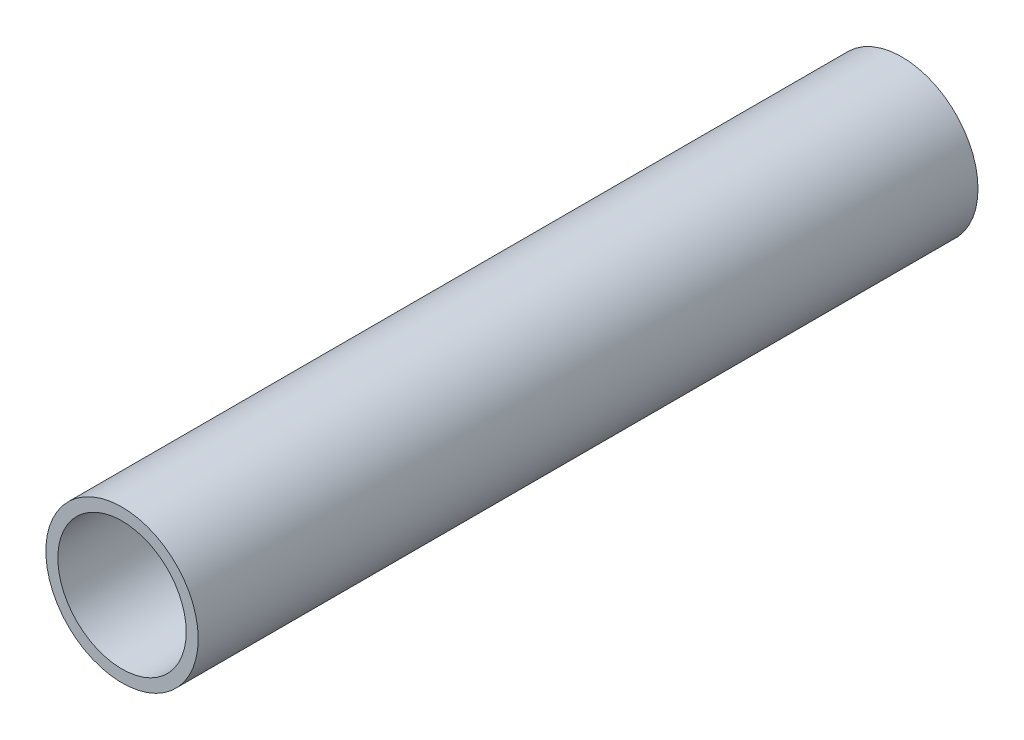
SolidWorks part; units mm, degrees
material "Hexcel AS4C (3000 Filaments)"
ref_plane "Front Plane" through (0, 0, 0) normal (0, 0, 1) x (1, 0, 0)
ref_plane "Top Plane" through (0, 0, 0) normal (0, 1, 0) x (1, 0, 0)
ref_plane "Right Plane" through (0, 0, 0) normal (1, 0, 0) x (0, 0, -1)
sketch "Sketch1" plane through (0, 0, 0) normal (0, 0, 1) x (1, 0, 0)
  circle A0 centre (0, 0) radius 12.7
  circle A1 centre (0, 0) radius 10.7
  dimension "D1" = 25.4
  dimension "D2" = 2
extrude "Boss-Extrude1" add sketch "Sketch1" along normal blind 130
